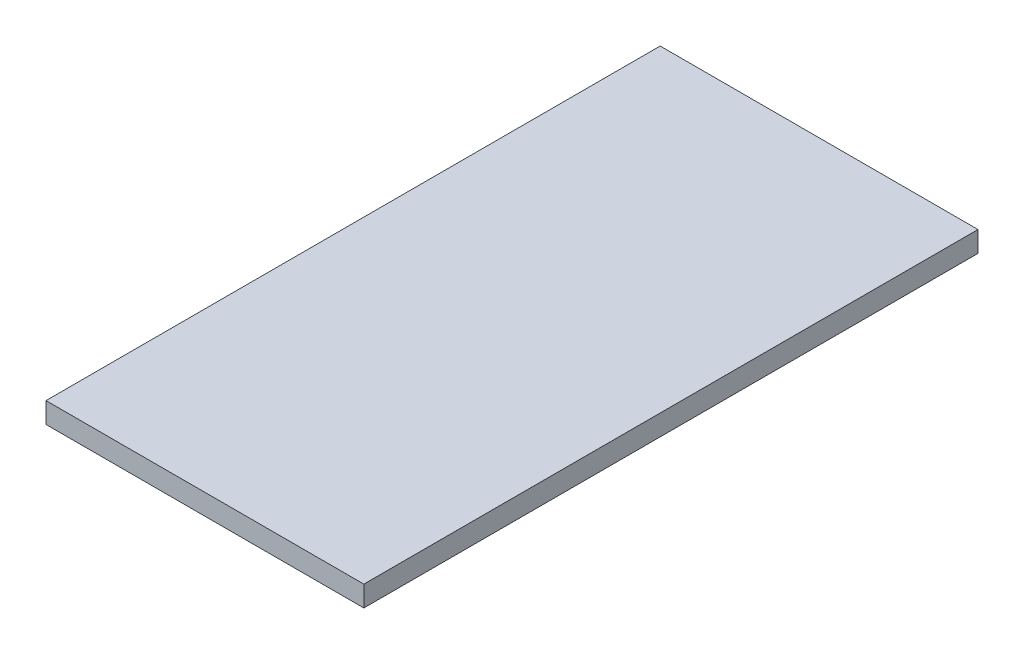
SolidWorks part; units mm, degrees
ref_plane "Front Plane" through (0, 0, 0) normal (0, 0, 1) x (1, 0, 0)
ref_plane "Top Plane" through (0, 0, 0) normal (0, 1, 0) x (1, 0, 0)
ref_plane "Right Plane" through (0, 0, 0) normal (1, 0, 0) x (0, 0, -1)
sketch "Sketch1" plane through (0, 0, 0) normal (0, 1, 0) x (1, 0, 0)
  line L1 (0, 0) -> (97.536, 0)
  line L2 (0, 0) -> (0, 188.468)
  line L3 (0, 188.468) -> (97.536, 188.468)
  line L4 (97.536, 0) -> (97.536, 188.468)
  dimension "D1" = 97.536
  dimension "D2" = 188.468
extrude "Boss-Extrude1" add sketch "Sketch1" along normal blind 6.35
